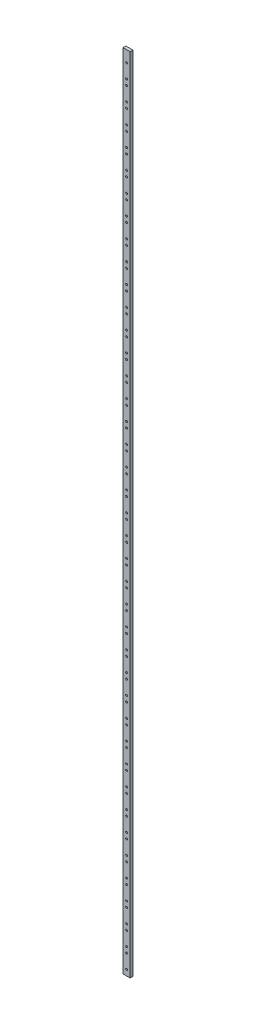
SolidWorks part; units mm, degrees
ref_plane "Front Plane" through (0, 0, 0) normal (0, 0, 1) x (1, 0, 0)
ref_plane "Top Plane" through (0, 0, 0) normal (0, 1, 0) x (1, 0, 0)
ref_plane "Right Plane" through (0, 0, 0) normal (1, 0, 0) x (0, 0, -1)
sketch "Sketch1" plane through (0, 0, 0) normal (0, 1, 0) x (1, 0, 0)
  line L1 (0, 0) -> (15.875, 0)
  line L2 (0, 0) -> (0, 6.35)
  line L3 (0, 6.35) -> (15.875, 6.35)
  line L4 (15.875, 0) -> (15.875, 6.35)
extrude "Boss-Extrude1" add sketch "Sketch1" along normal blind 1803.4
hole_wizard "Tap Drill for #10-32 Tap1" positions "Sketch5" profile "Sketch4" hole size "#10-32" standard "ANSI Inch" end condition through all
sketch "Sketch5" plane through (0, 0, 0) normal (0, 0, 1) x (1, 0, 0)
  line L0 (0, 0) -> (15.875, 0) construction
  line L1 (0, 1803.4) -> (0, 0) construction
  line L2 (7.9375, 44.45) -> (7.9375, 88.9) construction
  point P0 (7.9375, 12.7)
  point P9 (7.9375, 44.45)
  point P24 (7.9375, 57.15)
  point P25 (7.9375, 88.9)
  point P26 (7.9375, 101.6)
  point P27 (7.9375, 133.35)
  point P28 (7.9375, 146.05)
  point P29 (7.9375, 177.8)
  point P30 (7.9375, 190.5)
  point P31 (7.9375, 222.25)
  point P32 (7.9375, 234.95)
  point P33 (7.9375, 266.7)
  point P34 (7.9375, 279.4)
  point P35 (7.9375, 311.15)
  point P36 (7.9375, 323.85)
  point P37 (7.9375, 355.6)
  point P38 (7.9375, 368.3)
  point P39 (7.9375, 400.05)
  point P40 (7.9375, 412.75)
  point P41 (7.9375, 444.5)
  point P42 (7.9375, 457.2)
  point P43 (7.9375, 488.95)
  point P44 (7.9375, 501.65)
  point P45 (7.9375, 533.4)
  point P46 (7.9375, 546.1)
  point P47 (7.9375, 577.85)
  point P48 (7.9375, 590.55)
  point P49 (7.9375, 622.3)
  point P50 (7.9375, 635)
  point P51 (7.9375, 666.75)
  point P52 (7.9375, 679.45)
  point P53 (7.9375, 711.2)
  point P54 (7.9375, 723.9)
  point P55 (7.9375, 755.65)
  point P56 (7.9375, 768.35)
  point P57 (7.9375, 800.1)
  point P58 (7.9375, 812.8)
  point P59 (7.9375, 844.55)
  point P60 (7.9375, 857.25)
  point P61 (7.9375, 889)
  point P62 (7.9375, 901.7)
  point P63 (7.9375, 933.45)
  point P64 (7.9375, 946.15)
  point P65 (7.9375, 977.9)
  point P66 (7.9375, 990.6)
  point P67 (7.9375, 1022.35)
  point P68 (7.9375, 1035.05)
  point P69 (7.9375, 1066.8)
  point P70 (7.9375, 1079.5)
  point P71 (7.9375, 1111.25)
  point P72 (7.9375, 1123.95)
  point P73 (7.9375, 1155.7)
  point P74 (7.9375, 1168.4)
  point P75 (7.9375, 1200.15)
  point P76 (7.9375, 1212.85)
  point P77 (7.9375, 1244.6)
  point P78 (7.9375, 1257.3)
  point P79 (7.9375, 1289.05)
  point P80 (7.9375, 1301.75)
  point P81 (7.9375, 1333.5)
  point P82 (7.9375, 1346.2)
  point P83 (7.9375, 1377.95)
  point P84 (7.9375, 1390.65)
  point P85 (7.9375, 1422.4)
  point P86 (7.9375, 1435.1)
  point P87 (7.9375, 1466.85)
  point P88 (7.9375, 1479.55)
  point P89 (7.9375, 1511.3)
  point P90 (7.9375, 1524)
  point P91 (7.9375, 1555.75)
  point P92 (7.9375, 1568.45)
  point P93 (7.9375, 1600.2)
  point P94 (7.9375, 1612.9)
  point P95 (7.9375, 1644.65)
  point P96 (7.9375, 1657.35)
  point P97 (7.9375, 1689.1)
  point P98 (7.9375, 1701.8)
  point P99 (7.9375, 1733.55)
  point P100 (7.9375, 1746.25)
  point P101 (7.9375, 1778)
  dimension "D1" = 12.7
  dimension "D2" = 7.9375
  dimension "D3" = 31.75
  dimension "D5" = 44.45
  dimension "D4" = 40
sketch "Sketch4" plane through (7.9375, 12.7, 0) normal (1, 0, 0) x (0, -1, 0)
  line L0 (0, 0) -> (0, 6.35)
  line L1 (0, 6.35) -> (2.0193, 6.35)
  line L2 (2.0193, 6.35) -> (2.0193, 0)
  line L5 (2.0193, 0) -> (0, 0)
  line L11 (0, -6.35) -> (0, 107.95) construction
  dimension "Thru Hole Dia." = 4.0386
  dimension "Thru Hole Depth" = 6.35
